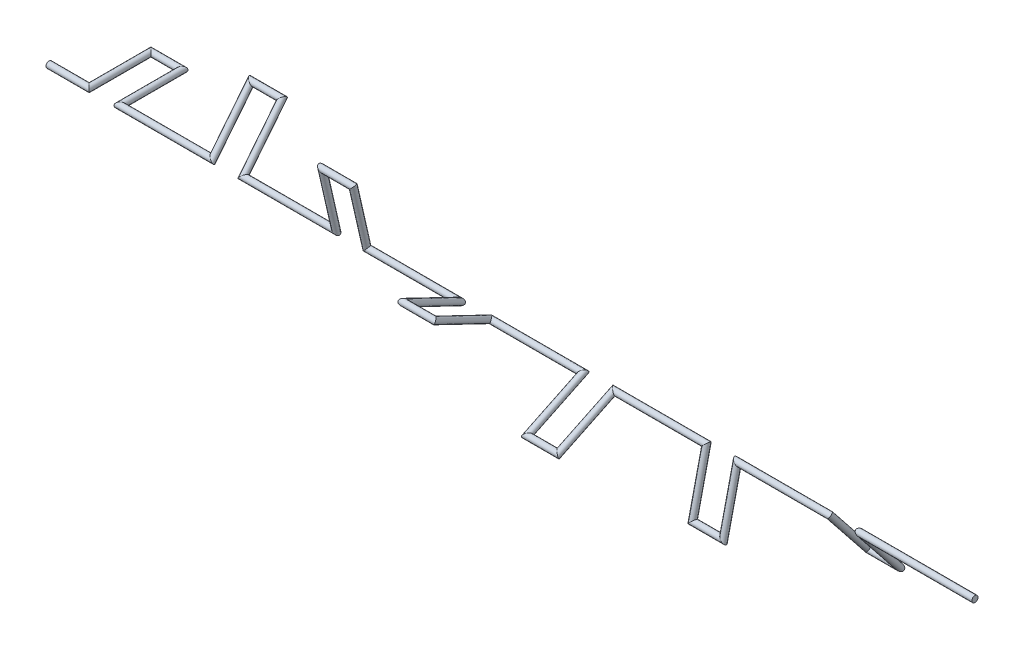
SolidWorks part; units mm, degrees
ref_plane "Front Plane" through (0, 0, 0) normal (0, 0, 1) x (1, 0, 0)
ref_plane "Top Plane" through (0, 0, 0) normal (0, 1, 0) x (1, 0, 0)
ref_plane "Right Plane" through (0, 0, 0) normal (1, 0, 0) x (0, 0, -1)
sketch "Sketch1" plane through (0, 0, 0) normal (0, 1, 0) x (1, 0, 0)
  line L0 (0, 0) -> (13, 0)
  line L1 (13, 0) -> (13, 20)
  line L2 (13, 20) -> (23, 20)
  line L3 (23, 20) -> (23, 0)
  line L4 (23, 0) -> (53, 0)
  point P3 (0, 0)
  dimension "D1" = 13
  dimension "D2" = 10
  dimension "D3" = 30
  dimension "D4" = 20
sketch "Sketch4" plane through (0, 0, 0) normal (1, 0, 0) x (0, 0, -1)
  line L0 (20, 0) -> (0, 0) construction
  line L1 (12.4698, -15.6366) -> (0, 0) construction
  line L2 (-4.4504, -19.4986) -> (0, 0) construction
  line L3 (-18.0194, -8.6777) -> (0, 0) construction
  line L4 (-18.0194, 8.6777) -> (0, 0) construction
  line L5 (-4.4504, 19.4986) -> (0, 0) construction
  line L6 (12.4698, 15.6366) -> (0, 0) construction
  circle A0 centre (0, 0) radius 20 construction
  point P12 (0, 0)
  dimension "D1" = 7
sketch3d "3DSketch1"
  line L0 (53, 0, 0) -> (53, 15.6366, -12.4698)
  line L1 (53, 15.6366, -12.4698) -> (63, 15.6366, -12.4698)
  line L2 (63, 15.6366, -12.4698) -> (63, 0, 0)
  line L3 (23, 0, 0) -> (53, 0, 0) construction
  line L5 (53, 0, 0) -> (23, 0, 0)
  line L6 (23, 0, 0) -> (23, 0, -20)
  line L7 (23, 0, -20) -> (13, 0, -20)
  line L8 (13, 0, -20) -> (13, 0, 0)
  line L9 (13, 0, 0) -> (0, 0, 0)
  line L10 (0, 15.6366, -12.4698) -> (0, 0, 0) construction
  line L11 (63, 0, 0) -> (93, 0, 0)
  line L12 (93, 0, 0) -> (93, 19.4986, 4.4504)
  line L13 (93, 19.4986, 4.4504) -> (103, 19.4986, 4.4504)
  line L14 (103, 19.4986, 4.4504) -> (103, 0, 0)
  line L15 (103, 0, 0) -> (133, 0, 0)
  line L16 (0, -8.6777, 18.0194) -> (0, 0, 0) construction
  line L17 (0, 19.4986, 4.4504) -> (0, 0, 0) construction
  line L18 (133, 0, 0) -> (133, 8.6777, 18.0194)
  line L19 (133, 8.6777, 18.0194) -> (143, 8.6777, 18.0194)
  line L20 (143, 8.6777, 18.0194) -> (143, 0, 0)
  line L21 (143, 0, 0) -> (173, 0, 0)
  line L22 (173, 0, 0) -> (173, -8.6777, 18.0194)
  line L23 (173, -8.6777, 18.0194) -> (183, -8.6777, 18.0194)
  line L24 (183, -8.6777, 18.0194) -> (183, 0, 0)
  line L25 (183, 0, 0) -> (213, 0, 0)
  line L26 (213, 0, 0) -> (213, -19.4986, 4.4504)
  line L27 (213, -19.4986, 4.4504) -> (223, -19.4986, 4.4504)
  line L28 (223, -19.4986, 4.4504) -> (223, 0, 0)
  line L29 (223, 0, 0) -> (253, 0, 0)
  line L30 (253, 0, 0) -> (253, -15.6366, -12.4698)
  line L31 (253, -15.6366, -12.4698) -> (263, -15.6366, -12.4698)
  line L32 (263, -15.6366, -12.4698) -> (263, 0, 0)
  line L33 (263, 0, 0) -> (300, 0, 0)
  line L34 (0, 8.6777, 18.0194) -> (0, 0, 0) construction
  line L36 (0, -19.4986, 4.4504) -> (0, 0, 0) construction
  line L37 (0, -15.6366, -12.4698) -> (0, 0, 0) construction
  point P42 (152.7618, 18.9912, -6.2716)
  point P45 (183, 15.9587, -12.0549)
  point P46 (183, -10.0375, 17.2988)
  point P47 (223, -19.7291, 3.2809)
  point P48 (263, -14.301, -13.9814)
  dimension "D1" = 10
  dimension "D2" = 20
  dimension "D6" = 300
sketch "Sketch5" plane through (0, 0, 0) normal (1, 0, 0) x (0, 0, -1)
  circle A0 centre (0, 0) radius 1
  dimension "D1" = 2
sweep "Sweep1" add profiles "Sketch5" path "3DSketch1"
sketch "Sketch3" plane through (0, 0, 0) normal (1, 0, 0) x (0, 0, -1)
  line L0 (20, 0) -> (0, 0)
  line L1 (0, 0) -> (12.4698, 15.6366)
  line L2 (0, 0) -> (20, 0)
  line L3 (0, 0) -> (12.4698, -15.6366)
  line L4 (0, 0) -> (-4.4504, -19.4986)
  line L5 (0, 0) -> (-18.0194, -8.6777)
  line L6 (0, 0) -> (-18.0194, 8.6777)
  line L7 (0, 0) -> (-4.4504, 19.4986)
  circle A0 centre (0, 0) radius 20
  point P16 (0, 0)
  dimension "D1" = 51.429
  dimension "D2" = 7
